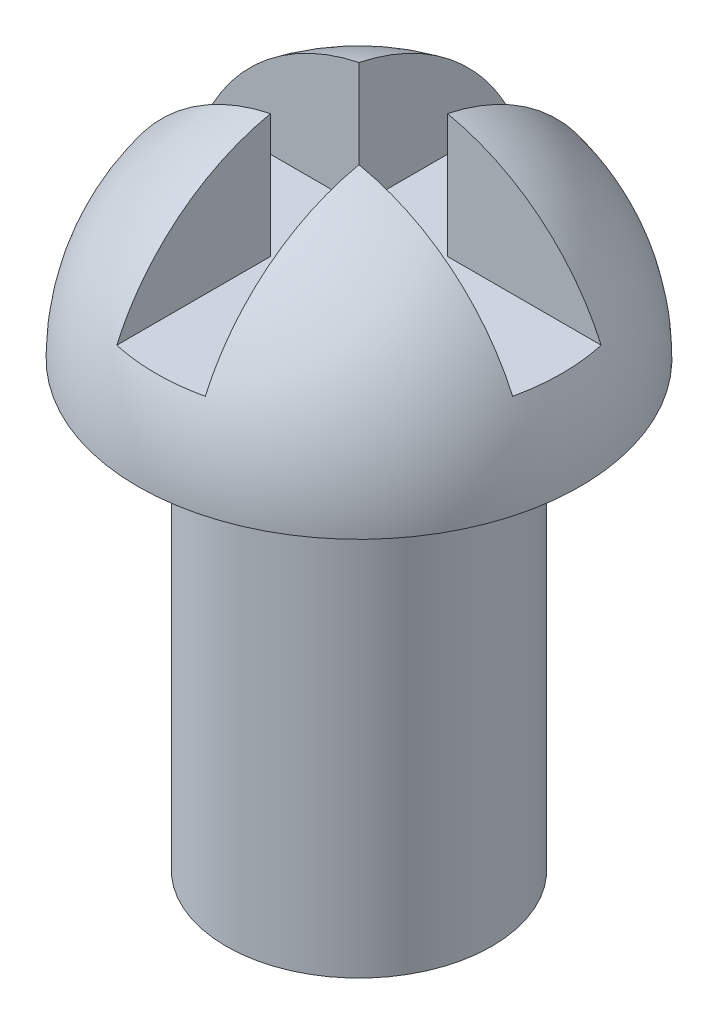
SolidWorks part; units mm, degrees
ref_plane "Front Plane" through (0, 0, 0) normal (0, 0, 1) x (1, 0, 0)
ref_plane "Top Plane" through (0, 0, 0) normal (0, 1, 0) x (1, 0, 0)
ref_plane "Right Plane" through (0, 0, 0) normal (1, 0, 0) x (0, 0, -1)
sketch "Sketch1" plane through (0, 0, 0) normal (0, 1, 0) x (1, 0, 0)
  circle A0 centre (0, 0) radius 1.5
  dimension "D1" = 3
extrude "Boss-Extrude1" add sketch "Sketch1" along normal blind 5
sketch "Sketch2" plane through (0, 5, 0) normal (0, 1, 0) x (1, 0, 0)
  line L0 (0, 2.5) -> (0, -2.5)
  arc A0 (0, -2.5) -> (0, 2.5) centre (0, 0) ccw
  dimension "D1" = 5
revolve "Revolve1" add sketch "Sketch2" angle 180 about L0
ref_plane "Plane1" through (0, 8, 0) normal (0, 1, 0) x (1, 0, 0)
sketch "Sketch3" plane through (0, 8, 0) normal (0, 1, 0) x (1, 0, 0)
  line L0 (-0.5, -0.5) -> (-0.5, -3.1286)
  line L1 (-0.5, 2.8714) -> (0.5, 2.8714)
  line L2 (-0.5, 2.8714) -> (-0.5, 0.5)
  line L3 (-0.5, -3.1286) -> (0.5, -3.1286)
  line L4 (0.5, 2.8714) -> (0.5, 0.5)
  line L5 (-3.0493, 0.5) -> (-0.5, 0.5)
  line L6 (-3.0493, 0.5) -> (-3.0493, -0.5)
  line L7 (-3.0493, -0.5) -> (-0.5, -0.5)
  line L8 (2.9507, 0.5) -> (2.9507, -0.5)
  line L9 (0.5, -0.5) -> (2.9507, -0.5)
  line L10 (0.5, -0.5) -> (0.5, -3.1286)
  line L11 (0.5, 0.5) -> (2.9507, 0.5)
  circle A0 centre (0, 0) radius 2.5 construction
  dimension "D1" = 1
  dimension "D2" = 6
  dimension "D3" = 1
  dimension "D4" = 6
  dimension "D5" = 0.5
  dimension "D6" = 0.5
extrude "Cut-Extrude1" cut sketch "Sketch3" against normal blind 2
